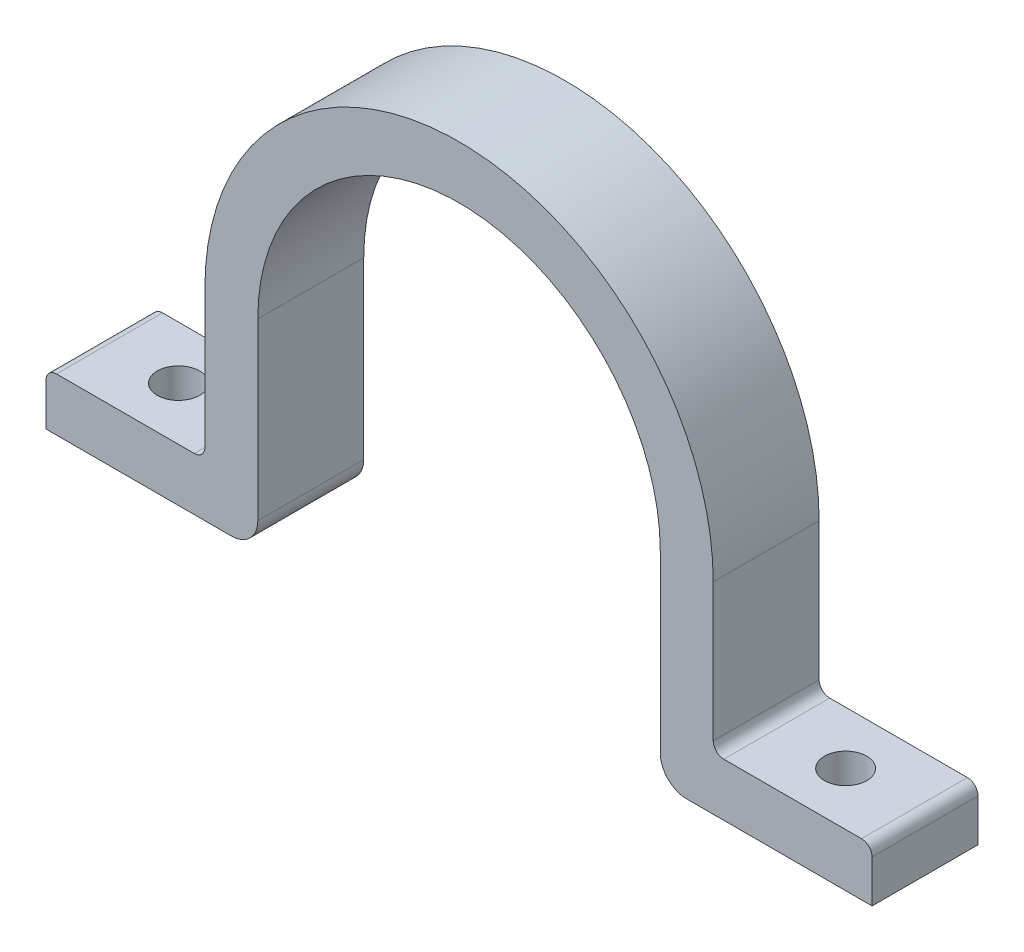
SolidWorks part; units mm, degrees
material "AISI 304"
ref_plane "Front Plane" through (0, 0, 0) normal (0, 0, 1) x (1, 0, 0)
ref_plane "Top Plane" through (0, 0, 0) normal (0, 1, 0) x (1, 0, 0)
ref_plane "Right Plane" through (0, 0, 0) normal (1, 0, 0) x (0, 0, -1)
sketch "Sketch1" plane through (0, 0, 0) normal (0, 0, 1) x (1, 0, 0)
  line L6 (-38, -38) -> (-78, -38)
  line L7 (38, -38) -> (78, -38)
  line L8 (-38, 0) -> (-38, -38)
  line L9 (38, 0) -> (38, -38)
  line L10 (-48, -28) -> (-78, -28)
  line L11 (-48, 0) -> (-48, -28)
  line L12 (48, 0) -> (48, -28)
  line L13 (48, -28) -> (78, -28)
  line L14 (-78, -28) -> (-78, -38)
  line L15 (78, -28) -> (78, -38)
  arc A1 (-38, 0) -> (38, 0) centre (0, 0) cw
  arc A2 (-48, 0) -> (48, 0) centre (0, 0) cw
  dimension "D1" = 38
  dimension "D2" = 10
  dimension "D3" = 30
  dimension "D5" = 38
  dimension "D4" = 30
extrude "Boss-Extrude1" add sketch "Sketch1" along normal blind 20
sketch "Sketch3" plane through (0, -28, 0) normal (0, 1, 0) x (1, 0, 0)
  line L0 (-48, 0) -> (-78, 0) construction
  line L1 (-78, -20) -> (-78, 0) construction
  line L2 (78, 0) -> (48, 0) construction
  circle A0 centre (-63, -10) radius 4
  circle A1 centre (63, -10) radius 4
  point P8 (-63, 0)
  point P11 (-78, -10)
  point P16 (63, 0)
  dimension "D1" = 8
extrude "Cut-Extrude2" cut sketch "Sketch3" against normal blind 20
fillet "Fillet3" radius 2 4 edges at (78, -28, 10) (48, -28, 10) (-78, -28, 10) (-48, -28, 10)
fillet "Fillet4" radius 5 2 edges at (38, -38, 10) (-38, -38, 10)
